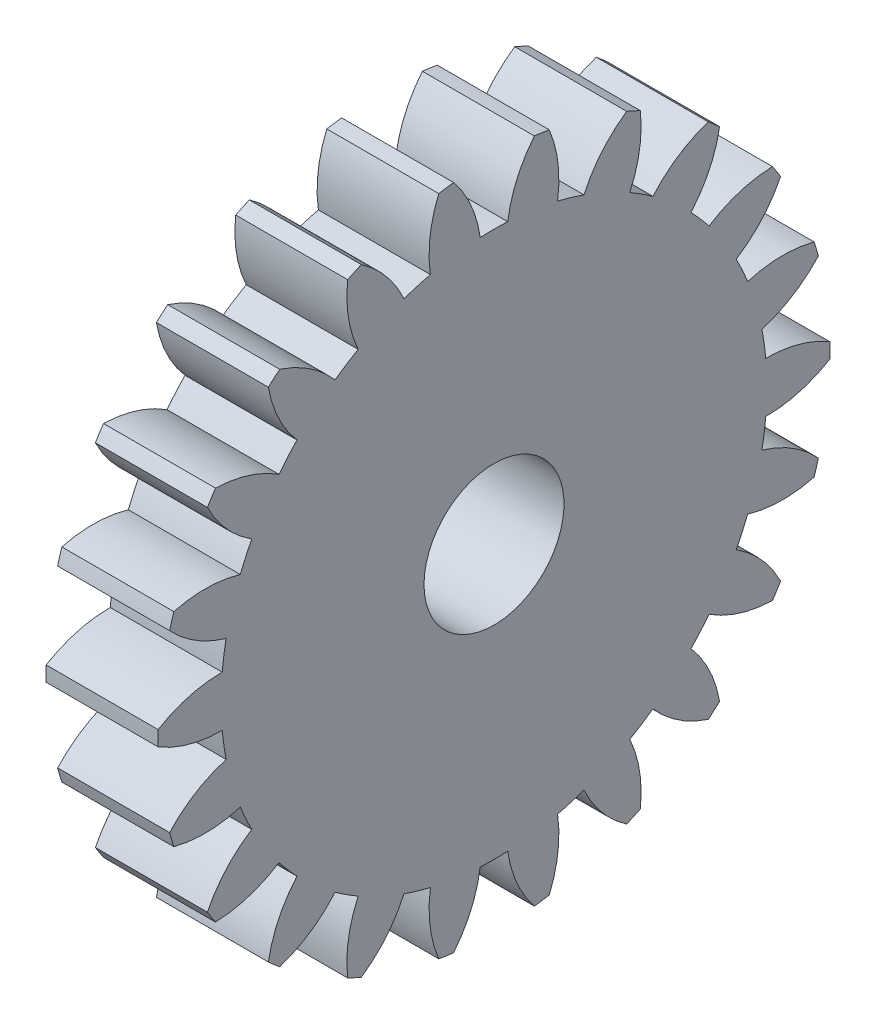
SolidWorks part; units mm, degrees
ref_plane "Plane1" through (0, 0, 0) normal (0, 0, 1) x (1, 0, 0)
ref_plane "Plane2" through (0, 0, 0) normal (0, 1, 0) x (1, 0, 0)
ref_plane "Plane3" through (0, 0, 0) normal (1, 0, 0) x (0, 0, -1)
sketch "HoldingSke" plane through (0, 0, 0) normal (0, 1, 0) x (1, 0, 0)
  line L0 (0, 0) -> (0.9272, -0.3746)
  line L1 (-15, 0) -> (100, 0) construction
  line L2 (0, 0) -> (-2.1039, 2.3779)
  line L3 (0, 0) -> (-11.863, 4.5341)
  line L4 (0, 0) -> (8.0072, 3.2351)
  line L5 (0, 0) -> (-46.8476, -17.4728)
  line L6 (0, 0) -> (-3.3159, -2.2372)
  line L7 (-2.1039, 2.3779) -> (8.6586, 51.2059)
  line L8 (-76.2, 54.61) -> (-75.3, 54.61)
  line L9 (-71.009, 38.7566) -> (-53.1078, 45.2721)
  line L10 (-76.2, 71.12) -> (104.1128, 71.12)
  line L11 (0, 0) -> (-4, 0)
  line L12 (-76.2, 101.6) -> (-76.162, 101.6)
  line L13 (24.9733, 27.94) -> (52.9518, 28.4284)
  line L14 (24.9733, 27.94) -> (24.9743, 27.94)
  line L15 (24.9733, 27.94) -> (100.4006, 29.5858)
  line L16 (-63.627, -1) -> (-12.827, -1)
  circle A0 centre (0, 0) radius 2.5
  circle A1 centre (0, 0) radius 9.749
  circle A2 centre (0, 0) radius 37.5
  circle A3 centre (0, 0) radius 2.5
  dimension "MHD" = 19.498
  dimension "Hub_dia" = 75
  dimension "Bore" = 5
  dimension "MBD" = 5
  dimension "Num_teeth" = 22
  dimension "Pitch" = 1
  dimension "Overall_len" = 50
  dimension "Show_teeth" = 22
  dimension "Thickness" = 4
  dimension "OAL" = 50.0001
  dimension "T_dim" = 0.9
  dimension "Ap" = 20
  dimension "H" = 19.05
  dimension "Pitch_radius" = 180.3128
  dimension "Width" = 4
  dimension "Backlash" = 0.038
  dimension "Addendum_fac" = 1
  dimension "Dedendum_fac" = 1.25
  dimension "Clearance_fac" = 0.25
  dimension "Dedendum_add" = 0.001
  dimension "Module" = 1
sketch "BasProSke" plane through (0, 0, 0) normal (0, 1, 0) x (1, 0, 0)
  line L0 (-10, 0) -> (60, 0) construction
  line L1 (0, 0) -> (0, 12)
  line L2 (0, 0) -> (4, 0)
  line L3 (4, 0) -> (4, 12)
  line L4 (4, 12) -> (0, 12)
  dimension "Thickness" = 4
  dimension "Diameter" = 24
revolve "Base-Revolve" add sketch "BasProSke" angle 360 about L0
sketch "TooCutSke" plane through (0, 0, 0) normal (1, 0, 0) x (0, 0, -1)
  line L1 (0, 0) -> (0, 107) construction
  line L2 (0, 0) -> (-0.8512, 10.967) construction
  line L3 (0, 0) -> (-3.1242, 21.7296) construction
  line L4 (-0.8512, 10.967) -> (-1.5621, 10.8648) construction
  arc A0 (0.491, 9.7366) -> (-0.491, 9.7366) centre (0, 0) ccw
  arc A1 (1.4609, 11.9363) -> (-1.4609, 11.9363) centre (0, 0) ccw
  circle A2 centre (0, 0) radius 11 construction
  circle A3 centre (0, 0) radius 10.3366 construction
  arc A4 (-0.491, 9.7366) -> (-1.4609, 11.9363) centre (-4.8488, 9.1288) ccw
  arc A5 (1.4609, 11.9363) -> (0.491, 9.7366) centre (4.8488, 9.1288) ccw
  dimension "Root_dia" = 19.498
  dimension "Overcut_dia" = 24.0508
  dimension "Pitch_dia" = 22
  dimension "Base_dia" = 20.6732
  dimension "Flank_rad" = 4.4
  dimension "Half_ang" = 8.182
  dimension "Half_CT" = 0.7182
extrude "ToothCut" cut sketch "TooCutSke" along normal through all
fillet "Breaks" [suppressed] radius 0.02
fillet "RootFillets" [suppressed] radius 0.251
pattern_circular "TeethCuts" count 22 every 16.364 about axis through (-10, 0, 0) along (1, 0, 0) of "ToothCut", "RootFillets", "Breaks"
sketch "HubNeaOneSke" plane through (0, 0, 0) normal (-1, 0, 0) x (0, 0, 1)
  circle A0 centre (0, 0) radius 9.749
  dimension "Diameter" = 19.498
extrude "HubNearOne" [suppressed] add sketch "HubNeaOneSke" along normal blind 46.0001
sketch "HubNeaBotSke" plane through (0, 0, 0) normal (-1, 0, 0) x (0, 0, 1)
  circle A0 centre (0, 0) radius 9.749
  dimension "Diameter" = 19.498
extrude "HubNearBoth" [suppressed] add sketch "HubNeaBotSke" along normal blind 23
ref_plane "FarPln" through (4, 0, 0) normal (1, 0, 0) x (0, 0, -1)
sketch "HubFarSke" plane through (4, 0, 0) normal (1, 0, 0) x (0, 0, -1)
  circle A0 centre (0, 0) radius 9.749
  dimension "Diameter" = 19.498
extrude "HubFar" [suppressed] add sketch "HubFarSke" along normal blind 23
sketch "BorSke" plane through (0, 0, 0) normal (1, 0, 0) x (0, 0, -1)
  circle A0 centre (0, 0) radius 2.5
  dimension "Diameter" = 5
extrude "Bore" cut sketch "BorSke" along normal mid plane 100.0001
sketch "KeySke" plane through (0, 0, 0) normal (1, 0, 0) x (0, 0, -1)
  line L0 (-1, 0) -> (-1, 3.4)
  line L1 (-1, 3.4) -> (1, 3.4)
  line L2 (1, 3.4) -> (1, 0)
  line L3 (0, 0) -> (0, 34) construction
  line L4 (-1, 0) -> (1, 0)
  dimension "Offset" = 3.4
  dimension "Width" = 2
extrude "Keyway" [suppressed] cut sketch "KeySke" along normal mid plane 100.0001
pattern_circular "Keyway2" [suppressed] count 2 every 90 about axis through (-10, 0, 0) along (1, 0, 0)
equation "' \"Module@HoldingSke\" = 6.35"
equation "' \"Num_teeth@HoldingSke\" = 12"
equation "' \"Ap@HoldingSke\" =  20"
equation "' \"Ap@HoldingSke\" = 20"
equation "' \"Width@HoldingSke\" = 0.5 * 25.4"
equation "' \"Hub_dia@HoldingSke\"= 1 * 25.4"
equation "' \"Hub_dia@HoldingSke\" = 1 * 25.4"
equation "' \"Overall_len@HoldingSke\" = 1.0 * 25.4"
equation "' \"Bore@HoldingSke\" = 0.75 * 25.4"
equation "' \"T_dim@HoldingSke\" = 0.1 * 25.4"
equation "' \"Width@KeySke\" = 0.25 * 25.4"
equation "' \"Show_teeth@HoldingSke\" = 13"
equation "' \"Backlash@HoldingSke\" = 0.009 * 25.4"
equation "' \"Addendum_fac@HoldingSke\" = 1.0"
equation "' \"Dedendum_fac@HoldingSke\" = 1.25"
equation "' \"Dedendum_add@HoldingSke\" = 0.00005 * 25.4"
equation "' \"Clearance_fac@HoldingSke\" = 0.25"
equation "\"Pitch@HoldingSke\" = 1 / \"Module@HoldingSke\""
equation "\"Overcut_dia@TooCutSke\" = (\"Num_teeth@HoldingSke\" + 2 * \"Addendum_fac@HoldingSke\") / \"Pitch@HoldingSke\" + 0.002 * 25.4"
equation "\"Pitch_dia@TooCutSke\" = \"Num_teeth@HoldingSke\" / \"Pitch@HoldingSke\""
equation "\"Base_dia@TooCutSke\" = \"Num_teeth@HoldingSke\" / \"Pitch@HoldingSke\" * cos((\"Ap@HoldingSke\"  * 3.14159265 / 180))"
equation "\"Root_dia@TooCutSke\" = (\"Num_teeth@HoldingSke\" + 2) / \"Pitch@HoldingSke\" - 2 * (\"Addendum_fac@HoldingSke\" + \"Dedendum_fac@HoldingSke\") / \"Pitch@HoldingSke\" - \"Dedendum_add@HoldingSke\" * 2"
equation "\"Half_ang@TooCutSke\" = 180 / \"Num_teeth@HoldingSke\""
equation "\"Half_CT@TooCutSke\" = \"Num_teeth@HoldingSke\" / \"Pitch@HoldingSke\" * sin((3.14159265 / 2 / \"Num_teeth@HoldingSke\")) / 2 - 7 * \"Backlash@HoldingSke\" / 4"
equation "\"Flank_rad@TooCutSke\" = \"Num_teeth@HoldingSke\" / \"Pitch@HoldingSke\" / 5"
equation "\"Radius@RootFillets\" = \"Clearance_fac@HoldingSke\" / \"Pitch@HoldingSke\" + \"Dedendum_add@HoldingSke\""
equation "\"Break_rad@Breaks\" = 0.02 / \"Pitch@HoldingSke\""
equation "\"Thickness@HoldingSke\" = \"Width@HoldingSke\""
equation "\"OAL@HoldingSke\" = \"Thickness@HoldingSke\""
equation "\"MHD@HoldingSke\" = (\"Num_teeth@HoldingSke\" + 2) / \"Pitch@HoldingSke\" - 2 * (\"Addendum_fac@HoldingSke\" + \"Dedendum_fac@HoldingSke\")  / \"Pitch@HoldingSke\" - \"Dedendum_add@HoldingSke\" * 2"
equation "\"MBD@HoldingSke\" = (\"Num_teeth@HoldingSke\" + 2) / \"Pitch@HoldingSke\" - 2 * (\"Addendum_fac@HoldingSke\" + \"Dedendum_fac@HoldingSke\")  / \"Pitch@HoldingSke\" - \"Dedendum_add@HoldingSke\" * 2 - 0.002 * 25.4"
equation "\"MHD@HoldingSke\" = ((sgn( \"MHD@HoldingSke\" - \"Hub_dia@HoldingSke\" )-1)*( \"MHD@HoldingSke\" - \"Hub_dia@HoldingSke\" ))/-2+ \"Hub_dia@HoldingSke\""
equation "\"MBD@HoldingSke\" = ((sgn( \"MBD@HoldingSke\" - \"Bore@HoldingSke\" )-1)*( \"MBD@HoldingSke\" - \"Bore@HoldingSke\" ))/-2+ \"Bore@HoldingSke\""
equation "\"OAL@HoldingSke\" = ((sgn( \"OAL@HoldingSke\" - \"Overall_len@HoldingSke\" )+1)*( \"OAL@HoldingSke\" - \"Overall_len@HoldingSke\" ))/2 + \"Overall_len@HoldingSke\" + 0.000002 * 25.4"
equation "\"Num_teeth@TeethCuts\" = int( \"Show_teeth@HoldingSke\" ) + 1"
equation "\"Num_teeth@TeethCuts\" = ((sgn( \"Num_teeth@TeethCuts\" - \"Num_teeth@HoldingSke\" )-1)*( \"Num_teeth@TeethCuts\" - \"Num_teeth@HoldingSke\" ))/-2+ \"Num_teeth@HoldingSke\""
equation "\"Num_teeth@TeethCuts\" = ((sgn( \"Num_teeth@TeethCuts\" - 2.0)+1)*( \"Num_teeth@TeethCuts\" - 2.0))/2 +2.0"
equation "\"Angle@TeethCuts\" = 360.0 / \"Num_teeth@HoldingSke\""
equation "\"Diameter@BasProSke\" = (\"Num_teeth@HoldingSke\" + 2 * \"Addendum_fac@HoldingSke\") / \"Pitch@HoldingSke\""
equation "\"Thickness@BasProSke\"  = \"Thickness@HoldingSke\""
equation "' \"Fillet_rad@BasProSke\" =  \"Thickness@HoldingSke\" * 0.05"
equation "' \"Fillet_rad@BasProSke\" = \"Thickness@HoldingSke\" * 0.05"
equation "\"MHD@HoldingSke\" = ((sgn( \"MHD@HoldingSke\" - \"Root_dia@TooCutSke\" )-1)*( \"MHD@HoldingSke\" - \"Root_dia@TooCutSke\" ))/-2+ \"Root_dia@TooCutSke\""
equation "\"Diameter@HubNeaOneSke\" = \"MHD@HoldingSke\""
equation "\"Length@HubNearOne\" = \"OAL@HoldingSke\" - \"Thickness@BasProSke\""
equation "\"Diameter@HubNeaBotSke\" = \"MHD@HoldingSke\""
equation "\"Length@HubNearBoth\" = ( \"OAL@HoldingSke\" - \"Thickness@BasProSke\" ) / 2.0"
equation "\"Thickness@FarPln\" = \"Thickness@BasProSke\""
equation "\"Diameter@HubFarSke\" = \"MHD@HoldingSke\""
equation "\"Length@HubFar\" = ( \"OAL@HoldingSke\" - \"Thickness@BasProSke\" ) / 2.0"
equation "\"Diameter@BorSke\" = \"MBD@HoldingSke\""
equation "\"D1@Bore\" = \"OAL@HoldingSke\" * 2.0"
equation "\"D1@Keyway\" = \"OAL@HoldingSke\" * 2.0"
equation "\"Offset@KeySke\" = \"T_dim@HoldingSke\" + \"MBD@HoldingSke\" / 2.0"
